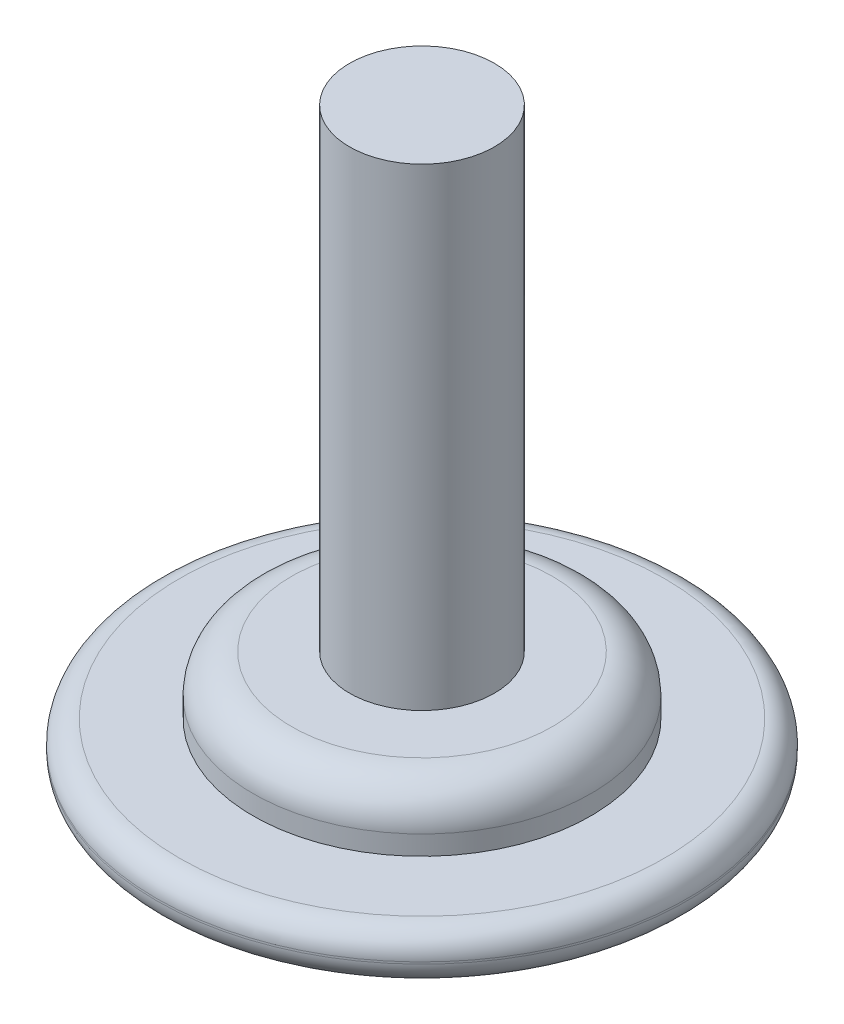
SolidWorks part; units mm, degrees
ref_plane "Front" through (0, 0, 0) normal (0, 0, 1) x (1, 0, 0)
ref_plane "Top" through (0, 0, 0) normal (0, 1, 0) x (1, 0, 0)
ref_plane "Right" through (0, 0, 0) normal (1, 0, 0) x (0, 0, -1)
sketch "Sketch1" plane through (0, 0, 0) normal (0, 0, 1) x (1, 0, 0)
  line L0 (0, 0) -> (0, 40.9972) construction
  line L1 (0, 0) -> (0, 38.1)
  line L2 (0, 38.1) -> (-4.7625, 38.1)
  line L3 (-4.7625, 38.1) -> (-4.7625, 6.985)
  line L4 (-4.7625, 6.985) -> (-11.1125, 6.985)
  line L5 (-11.1125, 6.985) -> (-11.1125, 3.175)
  line L6 (-11.1125, 3.175) -> (-17.4625, 3.175)
  line L7 (-17.4625, 3.175) -> (-17.4625, 0)
  line L8 (-17.4625, 0) -> (0, 0)
  dimension "D1" = 9.525
  dimension "D2" = 38.1
  dimension "D3" = 22.225
  dimension "D4" = 6.985
  dimension "D5" = 34.925
  dimension "D6" = 3.175
revolve "Base-Revolve" add sketch "Sketch1" angle 360 about L0
fillet "Fillet2" radius 1.524
fillet "Fillet3" radius 2.54
